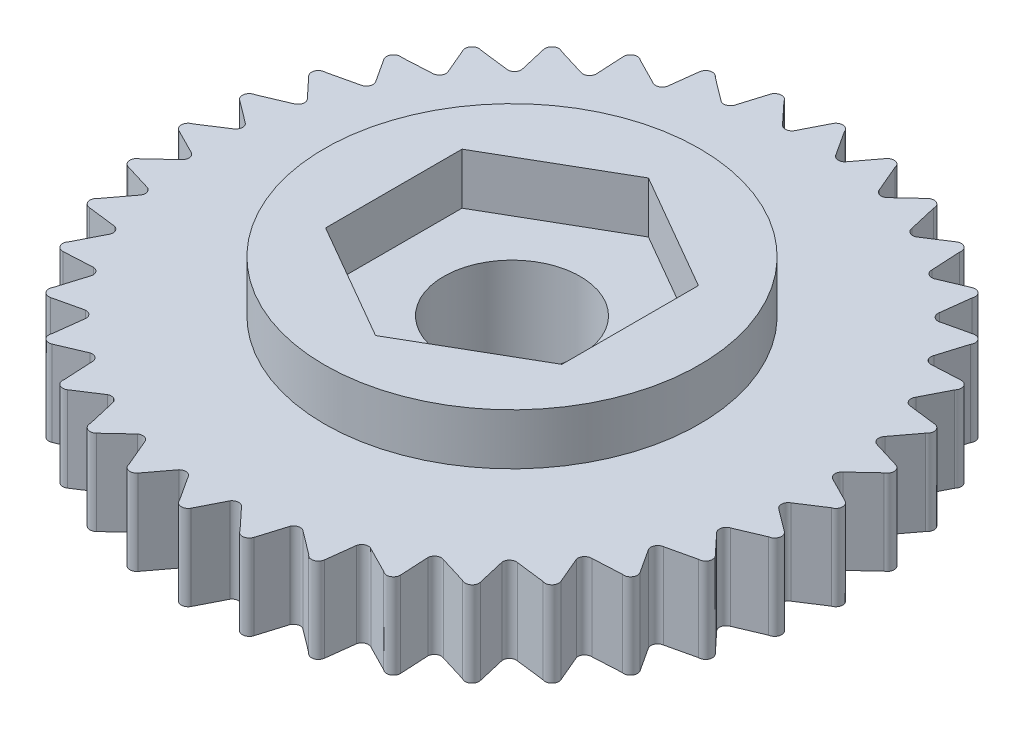
SolidWorks part; units mm, degrees
material "ABS"
ref_plane "Front Plane" through (0, 0, 0) normal (0, 0, 1) x (1, 0, 0)
ref_plane "Top Plane" through (0, 0, 0) normal (0, 1, 0) x (1, 0, 0)
ref_plane "Right Plane" through (0, 0, 0) normal (1, 0, 0) x (0, 0, -1)
sketch "Sketch1" plane through (0, 0, 0) normal (0, 1, 0) x (1, 0, 0)
  line L0 (-9.5, 0) -> (9.5, 0) construction
  line L1 (-0.7655, 8.75) -> (0.7655, 8.75) construction
  line L41 (-0.1803, 9.5909) -> (-0.5658, 8.8334) construction
  line L43 (0.1932, 9.5588) -> (0.6784, 8.8125) construction
  line L47 (-0.1803, 9.5909) -> (-0.5658, 8.8334)
  line L50 (0.1932, 9.5588) -> (0.6565, 8.8462)
  line L51 (1.4879, 9.4765) -> (0.9767, 8.7974)
  line L52 (1.8501, 9.38) -> (2.1826, 8.5978)
  line L53 (3.1109, 9.0742) -> (2.4895, 8.4942)
  line L54 (3.4508, 8.9163) -> (3.6425, 8.0881)
  line L55 (4.6393, 8.3961) -> (3.9267, 7.9328)
  line L56 (4.9467, 8.1816) -> (4.9916, 7.3328)
  line L57 (6.0268, 7.463) -> (5.2446, 7.1305)
  line L58 (6.2923, 7.1983) -> (6.1891, 6.3546)
  line L59 (7.2312, 6.303) -> (6.4031, 6.1114)
  line L60 (7.4466, 5.9963) -> (7.1985, 5.1833)
  line L61 (8.2159, 4.9516) -> (7.367, 4.9067)
  line L62 (8.3748, 4.6121) -> (7.9893, 3.8545)
  line L63 (8.9509, 3.4497) -> (8.1072, 3.5529)
  line L64 (9.0484, 3.0878) -> (8.5372, 2.4087)
  line L65 (9.4139, 1.843) -> (8.6009, 2.0911)
  line L66 (9.4471, 1.4696) -> (8.8258, 0.8896)
  line L67 (9.5909, 0.1803) -> (8.8334, 0.5658)
  line L68 (9.5588, -0.1932) -> (8.8462, -0.6565)
  line L69 (9.4765, -1.4879) -> (8.7974, -0.9767)
  line L70 (9.38, -1.8501) -> (8.5978, -2.1826)
  line L71 (9.0742, -3.1109) -> (8.4942, -2.4895)
  line L72 (8.9163, -3.4508) -> (8.0881, -3.6425)
  line L73 (8.3961, -4.6393) -> (7.9328, -3.9267)
  line L74 (8.1816, -4.9467) -> (7.3328, -4.9916)
  line L75 (7.463, -6.0268) -> (7.1305, -5.2446)
  line L76 (7.1983, -6.2923) -> (6.3546, -6.1891)
  line L77 (6.303, -7.2312) -> (6.1114, -6.4031)
  line L78 (5.9963, -7.4466) -> (5.1833, -7.1985)
  line L79 (4.9516, -8.2159) -> (4.9067, -7.367)
  line L80 (4.6121, -8.3748) -> (3.8545, -7.9893)
  line L81 (3.4497, -8.9509) -> (3.5529, -8.1072)
  line L82 (3.0878, -9.0484) -> (2.4087, -8.5372)
  line L83 (1.843, -9.4139) -> (2.0911, -8.6009)
  line L84 (1.4696, -9.4471) -> (0.8896, -8.8258)
  line L85 (0.1803, -9.5909) -> (0.5658, -8.8334)
  line L86 (-0.1932, -9.5588) -> (-0.6565, -8.8462)
  line L87 (-1.4879, -9.4765) -> (-0.9767, -8.7974)
  line L88 (-1.8501, -9.38) -> (-2.1826, -8.5978)
  line L89 (-3.1109, -9.0742) -> (-2.4895, -8.4942)
  line L90 (-3.4508, -8.9163) -> (-3.6425, -8.0881)
  line L91 (-4.6393, -8.3961) -> (-3.9267, -7.9328)
  line L92 (-4.9467, -8.1816) -> (-4.9916, -7.3328)
  line L93 (-6.0268, -7.463) -> (-5.2446, -7.1305)
  line L94 (-6.2923, -7.1983) -> (-6.1891, -6.3546)
  line L95 (-7.2312, -6.303) -> (-6.4031, -6.1114)
  line L96 (-7.4466, -5.9963) -> (-7.1985, -5.1833)
  line L97 (-8.2159, -4.9516) -> (-7.367, -4.9067)
  line L98 (-8.3748, -4.6121) -> (-7.9893, -3.8545)
  line L99 (-8.9509, -3.4497) -> (-8.1072, -3.5529)
  line L100 (-9.0484, -3.0878) -> (-8.5372, -2.4087)
  line L101 (-9.4139, -1.843) -> (-8.6009, -2.0911)
  line L102 (-9.4471, -1.4696) -> (-8.8258, -0.8896)
  line L103 (-9.5909, -0.1803) -> (-8.8334, -0.5658)
  line L104 (-9.5588, 0.1932) -> (-8.8462, 0.6565)
  line L105 (-9.4765, 1.4879) -> (-8.7974, 0.9767)
  line L106 (-9.38, 1.8501) -> (-8.5978, 2.1826)
  line L107 (-9.0742, 3.1109) -> (-8.4942, 2.4895)
  line L108 (-8.9163, 3.4508) -> (-8.0881, 3.6425)
  line L109 (-8.3961, 4.6393) -> (-7.9328, 3.9267)
  line L110 (-8.1816, 4.9467) -> (-7.3328, 4.9916)
  line L111 (-7.463, 6.0268) -> (-7.1305, 5.2446)
  line L112 (-7.1983, 6.2923) -> (-6.3546, 6.1891)
  line L113 (-6.303, 7.2312) -> (-6.1114, 6.4031)
  line L114 (-5.9963, 7.4466) -> (-5.1833, 7.1985)
  line L115 (-4.9516, 8.2159) -> (-4.9067, 7.367)
  line L116 (-4.6121, 8.3748) -> (-3.8545, 7.9893)
  line L117 (-3.4497, 8.9509) -> (-3.5529, 8.1072)
  line L118 (-3.0878, 9.0484) -> (-2.4087, 8.5372)
  line L119 (-1.843, 9.4139) -> (-2.0911, 8.6009)
  line L120 (-1.4696, 9.4471) -> (-0.8896, 8.8258)
  circle A1 centre (0, 0) radius 5.5
  arc A2 (-0.1803, 9.5909) -> (0.1932, 9.5588) centre (0, 9.5) cw
  arc A3 (-0.5658, 8.8334) -> (-0.7655, 8.75) centre (-0.7305, 8.9469) cw
  arc A4 (0.6565, 8.8462) -> (0.7655, 8.75) centre (0.8343, 8.9378) ccw
  arc A5 (0.9767, 8.7974) -> (0.7655, 8.75) centre (0.8343, 8.9378) cw
  arc A6 (1.4879, 9.4765) -> (1.8501, 9.38) centre (1.6497, 9.3557) cw
  arc A7 (2.1826, 8.5978) -> (2.2733, 8.4841) centre (2.3736, 8.6572) ccw
  arc A8 (2.4895, 8.4942) -> (2.2733, 8.4841) centre (2.3736, 8.6572) cw
  arc A9 (3.1109, 9.0742) -> (3.4508, 8.9163) centre (3.2492, 8.9271) cw
  arc A10 (3.6425, 8.0881) -> (3.712, 7.9605) centre (3.8409, 8.1135) ccw
  arc A11 (3.9267, 7.9328) -> (3.712, 7.9605) centre (3.8409, 8.1135) cw
  arc A12 (4.6393, 8.3961) -> (4.9467, 8.1816) centre (4.75, 8.2272) cw
  arc A13 (4.9916, 7.3328) -> (5.038, 7.195) centre (5.1914, 7.3233) ccw
  arc A14 (5.2446, 7.1305) -> (5.038, 7.195) centre (5.1914, 7.3233) cw
  arc A15 (6.0268, 7.463) -> (6.2923, 7.1983) centre (6.1065, 7.2774) cw
  arc A16 (6.1891, 6.3546) -> (6.2108, 6.2108) centre (6.3842, 6.3105) ccw
  arc A17 (6.4031, 6.1114) -> (6.2108, 6.2108) centre (6.3842, 6.3105) cw
  arc A18 (7.2312, 6.303) -> (7.4466, 5.9963) centre (7.2774, 6.1065) cw
  arc A19 (7.1985, 5.1833) -> (7.195, 5.038) centre (7.383, 5.106) ccw
  arc A20 (7.367, 4.9067) -> (7.195, 5.038) centre (7.383, 5.106) cw
  arc A21 (8.2159, 4.9516) -> (8.3748, 4.6121) centre (8.2272, 4.75) cw
  arc A22 (7.9893, 3.8545) -> (7.9605, 3.712) centre (8.1575, 3.7464) ccw
  arc A23 (8.1072, 3.5529) -> (7.9605, 3.712) centre (8.1575, 3.7464) cw
  arc A24 (8.9509, 3.4497) -> (9.0484, 3.0878) centre (8.9271, 3.2492) cw
  arc A25 (8.5372, 2.4087) -> (8.4841, 2.2733) centre (8.6841, 2.273) ccw
  arc A26 (8.6009, 2.0911) -> (8.4841, 2.2733) centre (8.6841, 2.273) cw
  arc A27 (9.4139, 1.843) -> (9.4471, 1.4696) centre (9.3557, 1.6497) cw
  arc A28 (8.8258, 0.8896) -> (8.75, 0.7655) centre (8.9469, 0.7305) ccw
  arc A29 (8.8334, 0.5658) -> (8.75, 0.7655) centre (8.9469, 0.7305) cw
  arc A30 (9.5909, 0.1803) -> (9.5588, -0.1932) centre (9.5, 0) cw
  arc A31 (8.8462, -0.6565) -> (8.75, -0.7655) centre (8.9378, -0.8343) ccw
  arc A32 (8.7974, -0.9767) -> (8.75, -0.7655) centre (8.9378, -0.8343) cw
  arc A33 (9.4765, -1.4879) -> (9.38, -1.8501) centre (9.3557, -1.6497) cw
  arc A34 (8.5978, -2.1826) -> (8.4841, -2.2733) centre (8.6572, -2.3736) ccw
  arc A35 (8.4942, -2.4895) -> (8.4841, -2.2733) centre (8.6572, -2.3736) cw
  arc A36 (9.0742, -3.1109) -> (8.9163, -3.4508) centre (8.9271, -3.2492) cw
  arc A37 (8.0881, -3.6425) -> (7.9605, -3.712) centre (8.1135, -3.8409) ccw
  arc A38 (7.9328, -3.9267) -> (7.9605, -3.712) centre (8.1135, -3.8409) cw
  arc A39 (8.3961, -4.6393) -> (8.1816, -4.9467) centre (8.2272, -4.75) cw
  arc A40 (7.3328, -4.9916) -> (7.195, -5.038) centre (7.3233, -5.1914) ccw
  arc A41 (7.1305, -5.2446) -> (7.195, -5.038) centre (7.3233, -5.1914) cw
  arc A42 (7.463, -6.0268) -> (7.1983, -6.2923) centre (7.2774, -6.1065) cw
  arc A43 (6.3546, -6.1891) -> (6.2108, -6.2108) centre (6.3105, -6.3842) ccw
  arc A44 (6.1114, -6.4031) -> (6.2108, -6.2108) centre (6.3105, -6.3842) cw
  arc A45 (6.303, -7.2312) -> (5.9963, -7.4466) centre (6.1065, -7.2774) cw
  arc A46 (5.1833, -7.1985) -> (5.038, -7.195) centre (5.106, -7.383) ccw
  arc A47 (4.9067, -7.367) -> (5.038, -7.195) centre (5.106, -7.383) cw
  arc A48 (4.9516, -8.2159) -> (4.6121, -8.3748) centre (4.75, -8.2272) cw
  arc A49 (3.8545, -7.9893) -> (3.712, -7.9605) centre (3.7464, -8.1575) ccw
  arc A50 (3.5529, -8.1072) -> (3.712, -7.9605) centre (3.7464, -8.1575) cw
  arc A51 (3.4497, -8.9509) -> (3.0878, -9.0484) centre (3.2492, -8.9271) cw
  arc A52 (2.4087, -8.5372) -> (2.2733, -8.4841) centre (2.273, -8.6841) ccw
  arc A53 (2.0911, -8.6009) -> (2.2733, -8.4841) centre (2.273, -8.6841) cw
  arc A54 (1.843, -9.4139) -> (1.4696, -9.4471) centre (1.6497, -9.3557) cw
  arc A55 (0.8896, -8.8258) -> (0.7655, -8.75) centre (0.7305, -8.9469) ccw
  arc A56 (0.5658, -8.8334) -> (0.7655, -8.75) centre (0.7305, -8.9469) cw
  arc A57 (0.1803, -9.5909) -> (-0.1932, -9.5588) centre (0, -9.5) cw
  arc A58 (-0.6565, -8.8462) -> (-0.7655, -8.75) centre (-0.8343, -8.9378) ccw
  arc A59 (-0.9767, -8.7974) -> (-0.7655, -8.75) centre (-0.8343, -8.9378) cw
  arc A60 (-1.4879, -9.4765) -> (-1.8501, -9.38) centre (-1.6497, -9.3557) cw
  arc A61 (-2.1826, -8.5978) -> (-2.2733, -8.4841) centre (-2.3736, -8.6572) ccw
  arc A62 (-2.4895, -8.4942) -> (-2.2733, -8.4841) centre (-2.3736, -8.6572) cw
  arc A63 (-3.1109, -9.0742) -> (-3.4508, -8.9163) centre (-3.2492, -8.9271) cw
  arc A64 (-3.6425, -8.0881) -> (-3.712, -7.9605) centre (-3.8409, -8.1135) ccw
  arc A65 (-3.9267, -7.9328) -> (-3.712, -7.9605) centre (-3.8409, -8.1135) cw
  arc A66 (-4.6393, -8.3961) -> (-4.9467, -8.1816) centre (-4.75, -8.2272) cw
  arc A67 (-4.9916, -7.3328) -> (-5.038, -7.195) centre (-5.1914, -7.3233) ccw
  arc A68 (-5.2446, -7.1305) -> (-5.038, -7.195) centre (-5.1914, -7.3233) cw
  arc A69 (-6.0268, -7.463) -> (-6.2923, -7.1983) centre (-6.1065, -7.2774) cw
  arc A70 (-6.1891, -6.3546) -> (-6.2108, -6.2108) centre (-6.3842, -6.3105) ccw
  arc A71 (-6.4031, -6.1114) -> (-6.2108, -6.2108) centre (-6.3842, -6.3105) cw
  arc A72 (-7.2312, -6.303) -> (-7.4466, -5.9963) centre (-7.2774, -6.1065) cw
  arc A73 (-7.1985, -5.1833) -> (-7.195, -5.038) centre (-7.383, -5.106) ccw
  arc A74 (-7.367, -4.9067) -> (-7.195, -5.038) centre (-7.383, -5.106) cw
  arc A75 (-8.2159, -4.9516) -> (-8.3748, -4.6121) centre (-8.2272, -4.75) cw
  arc A76 (-7.9893, -3.8545) -> (-7.9605, -3.712) centre (-8.1575, -3.7464) ccw
  arc A77 (-8.1072, -3.5529) -> (-7.9605, -3.712) centre (-8.1575, -3.7464) cw
  arc A78 (-8.9509, -3.4497) -> (-9.0484, -3.0878) centre (-8.9271, -3.2492) cw
  arc A79 (-8.5372, -2.4087) -> (-8.4841, -2.2733) centre (-8.6841, -2.273) ccw
  arc A80 (-8.6009, -2.0911) -> (-8.4841, -2.2733) centre (-8.6841, -2.273) cw
  arc A81 (-9.4139, -1.843) -> (-9.4471, -1.4696) centre (-9.3557, -1.6497) cw
  arc A82 (-8.8258, -0.8896) -> (-8.75, -0.7655) centre (-8.9469, -0.7305) ccw
  arc A83 (-8.8334, -0.5658) -> (-8.75, -0.7655) centre (-8.9469, -0.7305) cw
  arc A84 (-9.5909, -0.1803) -> (-9.5588, 0.1932) centre (-9.5, 0) cw
  arc A85 (-8.8462, 0.6565) -> (-8.75, 0.7655) centre (-8.9378, 0.8343) ccw
  arc A86 (-8.7974, 0.9767) -> (-8.75, 0.7655) centre (-8.9378, 0.8343) cw
  arc A87 (-9.4765, 1.4879) -> (-9.38, 1.8501) centre (-9.3557, 1.6497) cw
  arc A88 (-8.5978, 2.1826) -> (-8.4841, 2.2733) centre (-8.6572, 2.3736) ccw
  arc A89 (-8.4942, 2.4895) -> (-8.4841, 2.2733) centre (-8.6572, 2.3736) cw
  arc A90 (-9.0742, 3.1109) -> (-8.9163, 3.4508) centre (-8.9271, 3.2492) cw
  arc A91 (-8.0881, 3.6425) -> (-7.9605, 3.712) centre (-8.1135, 3.8409) ccw
  arc A92 (-7.9328, 3.9267) -> (-7.9605, 3.712) centre (-8.1135, 3.8409) cw
  arc A93 (-8.3961, 4.6393) -> (-8.1816, 4.9467) centre (-8.2272, 4.75) cw
  arc A94 (-7.3328, 4.9916) -> (-7.195, 5.038) centre (-7.3233, 5.1914) ccw
  arc A95 (-7.1305, 5.2446) -> (-7.195, 5.038) centre (-7.3233, 5.1914) cw
  arc A96 (-7.463, 6.0268) -> (-7.1983, 6.2923) centre (-7.2774, 6.1065) cw
  arc A97 (-6.3546, 6.1891) -> (-6.2108, 6.2108) centre (-6.3105, 6.3842) ccw
  arc A98 (-6.1114, 6.4031) -> (-6.2108, 6.2108) centre (-6.3105, 6.3842) cw
  arc A99 (-6.303, 7.2312) -> (-5.9963, 7.4466) centre (-6.1065, 7.2774) cw
  arc A100 (-5.1833, 7.1985) -> (-5.038, 7.195) centre (-5.106, 7.383) ccw
  arc A101 (-4.9067, 7.367) -> (-5.038, 7.195) centre (-5.106, 7.383) cw
  arc A102 (-4.9516, 8.2159) -> (-4.6121, 8.3748) centre (-4.75, 8.2272) cw
  arc A103 (-3.8545, 7.9893) -> (-3.712, 7.9605) centre (-3.7464, 8.1575) ccw
  arc A104 (-3.5529, 8.1072) -> (-3.712, 7.9605) centre (-3.7464, 8.1575) cw
  arc A105 (-3.4497, 8.9509) -> (-3.0878, 9.0484) centre (-3.2492, 8.9271) cw
  arc A106 (-2.4087, 8.5372) -> (-2.2733, 8.4841) centre (-2.273, 8.6841) ccw
  arc A107 (-2.0911, 8.6009) -> (-2.2733, 8.4841) centre (-2.273, 8.6841) cw
  arc A108 (-1.843, 9.4139) -> (-1.4696, 9.4471) centre (-1.6497, 9.3557) cw
  arc A109 (-0.8896, 8.8258) -> (-0.7655, 8.75) centre (-0.7305, 8.9469) ccw
  point P453 (0, 0)
  dimension "D2" = 11
  dimension "D7" = 0.2019
  dimension "D8" = 0.2
  dimension "D9" = 19
  dimension "D3" = 0.75
  dimension "D4" = 60
  dimension "D5" = 0.85
  dimension "D6" = 0.85
  dimension "D10" = 36
extrude "Boss-Extrude1" add sketch "Sketch1" along normal blind 2.5
sketch "Sketch2" plane through (0, 0, 0) normal (0, 1, 0) x (1, 0, 0)
  line L0 (0, 4.0025) -> (0, -4.0025) construction
  line L1 (0, 4.0025) -> (-3.4663, 2.0013)
  line L2 (-3.4663, 2.0013) -> (-3.4663, -2.0013)
  line L3 (-3.4663, -2.0013) -> (0, -4.0025)
  line L4 (0, -4.0025) -> (3.4663, -2.0013)
  line L5 (3.4663, -2.0013) -> (3.4663, 2.0013)
  line L6 (3.4663, 2.0013) -> (0, 4.0025)
  circle A0 centre (0, 0) radius 5.5 construction
  circle A1 centre (0, 0) radius 5.5
  circle A2 centre (0, 0) radius 4.0025 construction
  dimension "D1" = 8.005
extrude "Boss-Extrude2" add sketch "Sketch2" along normal blind 4
sketch "Sketch3" plane through (0, 0, 0) normal (0, 1, 0) x (1, 0, 0)
  line L0 (3.4663, 2.0013) -> (0, 4.0025) construction
  line L1 (0, 4.0025) -> (-3.4663, 2.0013) construction
  line L2 (3.4663, -2.0013) -> (3.4663, 2.0013) construction
  line L3 (0, -4.0025) -> (3.4663, -2.0013) construction
  line L4 (-3.4663, -2.0013) -> (0, -4.0025) construction
  line L5 (-3.4663, 2.0013) -> (-3.4663, -2.0013) construction
  line L6 (0, 4.0025) -> (-3.4663, 2.0013)
  line L7 (3.4663, 2.0013) -> (0, 4.0025)
  line L8 (3.4663, -2.0013) -> (3.4663, 2.0013)
  line L9 (0, -4.0025) -> (3.4663, -2.0013)
  line L10 (-3.4663, -2.0013) -> (0, -4.0025)
  line L11 (-3.4663, 2.0013) -> (-3.4663, -2.0013)
  circle A0 centre (0, 0) radius 2.0025
  dimension "D1" = 4.005
extrude "Boss-Extrude3" add sketch "Sketch3" along normal blind 2.5
sketch "Axis" plane through (0, 0, 0) normal (1, 0, 0) x (0, 0, -1)
  line L0 (0, 0) -> (0, 4) construction
  line L1 (5.5, 4) -> (-5.5, 4) construction
